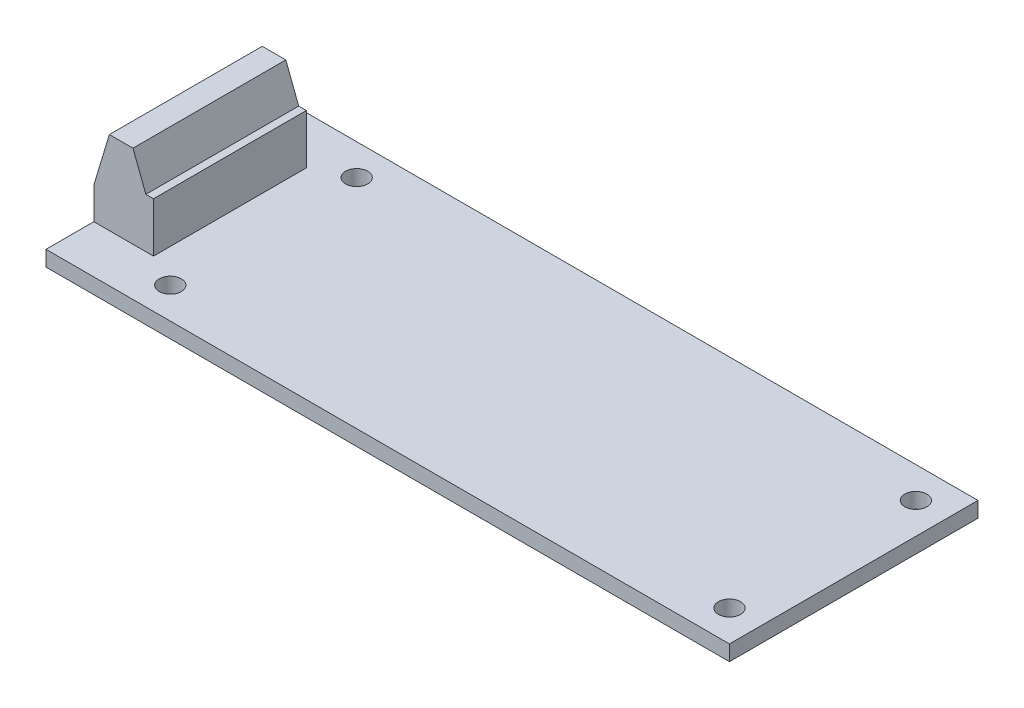
SolidWorks part; units mm, degrees
ref_plane "Front Plane" through (0, 0, 0) normal (0, 0, 1) x (1, 0, 0)
ref_plane "Top Plane" through (0, 0, 0) normal (0, 1, 0) x (1, 0, 0)
ref_plane "Right Plane" through (0, 0, 0) normal (1, 0, 0) x (0, 0, -1)
sketch "Sketch2" plane through (0, 0, 0) normal (0, 1, 0) x (1, 0, 0)
  line L1 (0, 0) -> (69.85, 0)
  line L2 (0, 0) -> (0, 25.4)
  line L3 (0, 25.4) -> (69.85, 25.4)
  line L4 (69.85, 0) -> (69.85, 25.4)
  dimension "D1" = 69.85
  dimension "D2" = 25.4
extrude "Boss-Extrude1" add sketch "Sketch2" along normal blind 1.5748
hole_wizard "Tap Drill for #4-40 Tap1" positions "3DSketch1" profile "Sketch3" hole size "#4-40" standard "ANSI Inch" end condition through all
sketch3d "3DSketch1"
  line L0 (69.85, 1.5748, 0) -> (69.85, 1.5748, -25.4) construction
  line L1 (69.85, 1.5748, -25.4) -> (0, 1.5748, -25.4) construction
  line L2 (0, 1.5748, 0) -> (69.85, 1.5748, 0) construction
  line L3 (0, 1.5748, -25.4) -> (0, 1.5748, 0) construction
  point P0 (9.525, 1.5748, -22.225)
  point P2 (9.525, 1.5748, -3.175)
  point P4 (66.675, 1.5748, -3.175)
  point P6 (66.675, 1.5748, -22.225)
  dimension "D1" = 3.175
  dimension "D2" = 3.175
  dimension "D3" = 3.175
  dimension "D4" = 3.175
  dimension "D5" = 3.175
  dimension "D6" = 3.175
  dimension "D7" = 9.525
  dimension "D8" = 9.525
sketch "Sketch3" plane through (9.525, 1.5748, -22.225) normal (1, 0, 0) x (0, 0, 1)
  line L0 (0, 0) -> (0, 1.5748)
  line L1 (0, 1.5748) -> (1.1303, 1.5748)
  line L2 (1.1303, 1.5748) -> (1.1303, 0)
  line L5 (1.1303, 0) -> (0, 0)
  line L11 (0, -6.35) -> (0, 107.95) construction
  dimension "Thru Hole Dia." = 2.2606
  dimension "Thru Hole Depth" = 1.5748
ref_plane "Plane1" through (0, 0, -12.7) normal (0, 0, 1) x (1, 0, 0)
sketch "Sketch4" plane through (0, 0, -12.7) normal (0, 0, 1) x (1, 0, 0)
  line L0 (0, 1.5748) -> (0, 4.8179)
  line L1 (0, 4.8179) -> (1.5885, 10.0838)
  line L2 (1.5885, 10.0838) -> (3.9995, 10.0838)
  line L3 (3.9995, 10.0838) -> (5.315, 6.6548)
  line L4 (5.315, 6.6548) -> (6.096, 6.6548)
  line L5 (6.096, 6.6548) -> (6.096, 1.5748)
  line L6 (6.096, 1.5748) -> (0, 1.5748)
  line L8 (0, 1.5748) -> (69.85, 1.5748) construction
  point P12 (2.794, 10.0838)
  dimension "D1" = 5.08
  dimension "D2" = 6.096
  dimension "D3" = 2.794
  dimension "D4" = 8.509
extrude "Boss-Extrude2" add sketch "Sketch4" along normal mid plane 15.621
